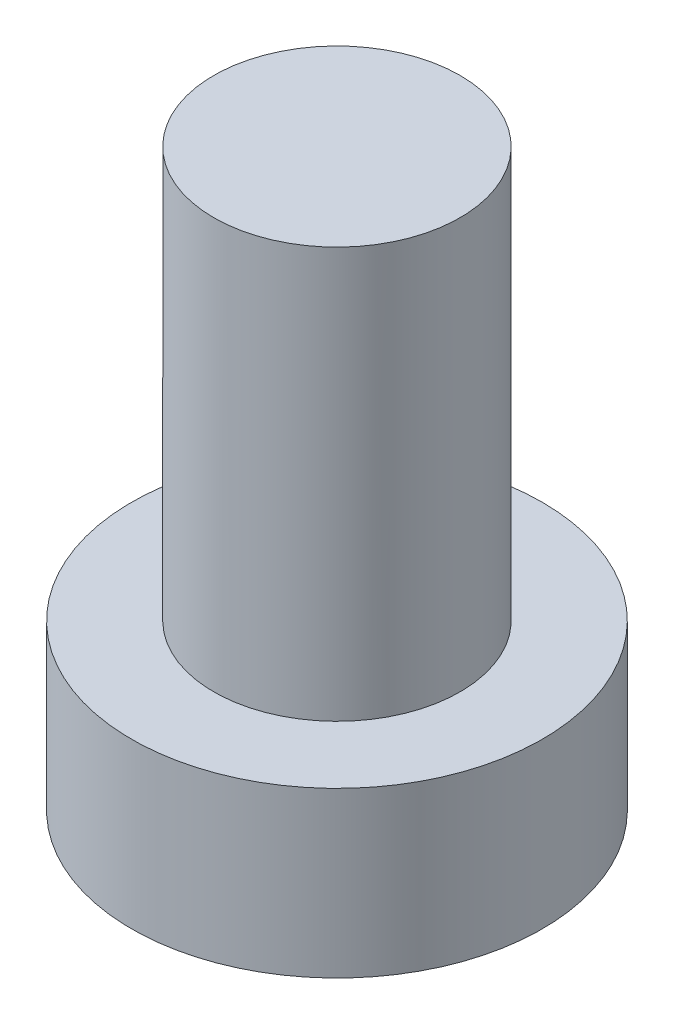
SolidWorks part; units mm, degrees
material "1060 Alloy"
ref_plane "Front Plane" through (0, 0, 0) normal (0, 0, 1) x (1, 0, 0)
ref_plane "Top Plane" through (0, 0, 0) normal (0, 1, 0) x (1, 0, 0)
ref_plane "Right Plane" through (0, 0, 0) normal (1, 0, 0) x (0, 0, -1)
sketch "Sketch1" plane through (0, 0, 0) normal (0, 1, 0) x (1, 0, 0)
  circle A0 centre (0, 0) radius 3
  dimension "D1" = 6
extrude "Extrude1" add sketch "Sketch1" along normal blind 10
sketch "Sketch2" plane through (0, 0, 0) normal (0, -1, 0) x (1, 0, 0)
  circle A0 centre (0, 0) radius 5
  dimension "D1" = 10
extrude "Extrude2" add sketch "Sketch2" along normal blind 4
